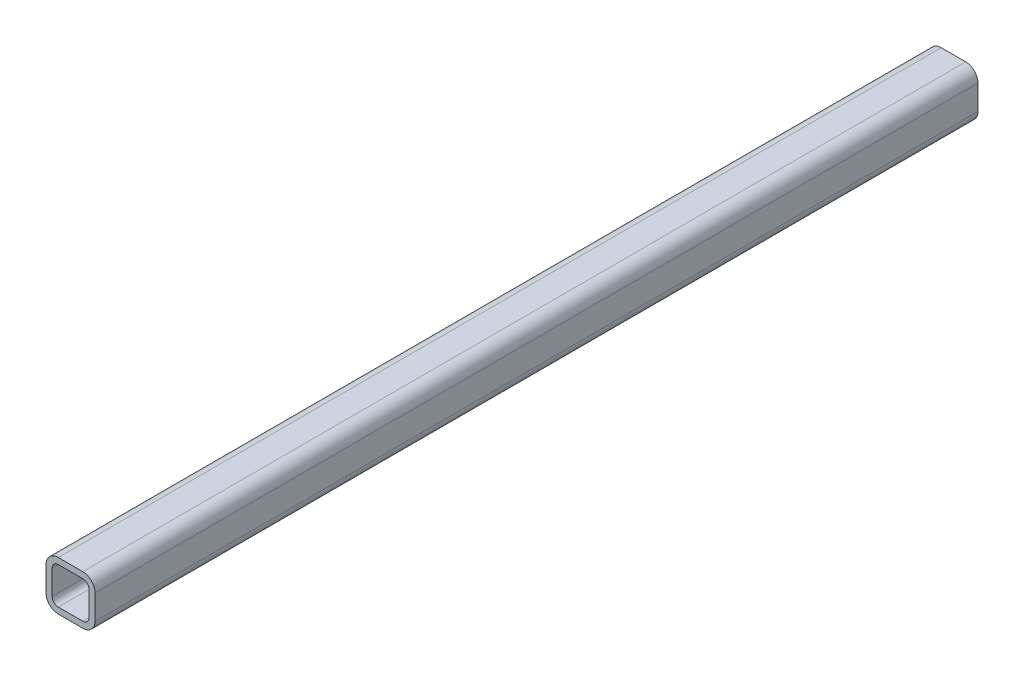
SolidWorks part; units mm, degrees
ref_plane "Front Plane" through (0, 0, 0) normal (0, 0, 1) x (1, 0, 0)
ref_plane "Top Plane" through (0, 0, 0) normal (0, 1, 0) x (1, 0, 0)
ref_plane "Right Plane" through (0, 0, 0) normal (1, 0, 0) x (0, 0, -1)
sketch "Sketch1" plane through (0, 0, 0) normal (0, 0, 1) x (1, 0, 0)
  line L0 (12.7, 6.35) -> (38.1, 6.35)
  line L1 (6.35, 12.7) -> (6.35, 38.1)
  line L2 (38.1, 44.45) -> (12.7, 44.45)
  line L3 (44.45, 38.1) -> (44.45, 12.7)
  line L4 (12.7, 0) -> (38.1, 0)
  line L5 (0, 12.7) -> (0, 38.1)
  line L6 (38.1, 50.8) -> (12.7, 50.8)
  line L7 (50.8, 38.1) -> (50.8, 12.7)
  arc A0 (50.8, 38.1) -> (38.1, 50.8) centre (38.1, 38.1) ccw
  arc A1 (38.1, 0) -> (50.8, 12.7) centre (38.1, 12.7) ccw
  arc A2 (0, 12.7) -> (12.7, 0) centre (12.7, 12.7) ccw
  arc A3 (12.7, 50.8) -> (0, 38.1) centre (12.7, 38.1) ccw
  arc A4 (12.7, 44.45) -> (6.35, 38.1) centre (12.7, 38.1) ccw
  arc A5 (44.45, 38.1) -> (38.1, 44.45) centre (38.1, 38.1) ccw
  arc A6 (38.1, 6.35) -> (44.45, 12.7) centre (38.1, 12.7) ccw
  arc A7 (6.35, 12.7) -> (12.7, 6.35) centre (12.7, 12.7) ccw
  dimension "D1" = 12.7
  dimension "Thickness" = 6.35
  dimension "V_leg" = 50.8
  dimension "H_leg" = 50.8
extrude "Boss-Extrude1" add sketch "Sketch1" along normal mid plane 914.4
